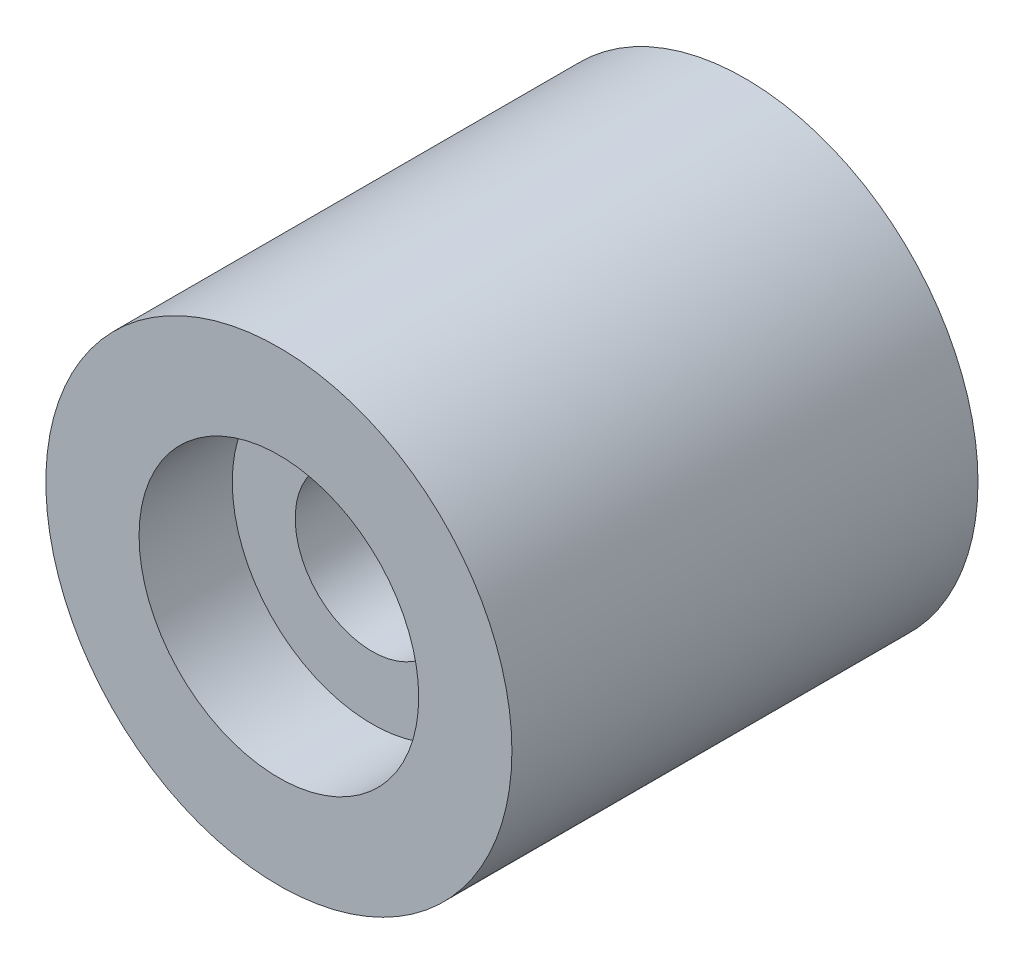
SolidWorks part; units mm, degrees
ref_plane "Front Plane" through (0, 0, 0) normal (0, 0, 1) x (1, 0, 0)
ref_plane "Top Plane" through (0, 0, 0) normal (0, 1, 0) x (1, 0, 0)
ref_plane "Right Plane" through (0, 0, 0) normal (1, 0, 0) x (0, 0, -1)
sketch "Sketch1" plane through (0, 0, 0) normal (0, 0, 1) x (1, 0, 0)
  circle A0 centre (0, 0) radius 5
  dimension "D1" = 10
extrude "Boss-Extrude1" add sketch "Sketch1" along normal blind 10
sketch "Sketch2" plane through (0, 0, 0) normal (0, 0, 1) x (1, 0, 0)
  circle A0 centre (0, 0) radius 3
  dimension "D1" = 6
extrude "Cut-Extrude1" cut sketch "Sketch2" along normal blind 2
sketch "Sketch3" plane through (0, 0, 0) normal (0, 0, 1) x (1, 0, 0)
  circle A0 centre (0, 0) radius 1.65
  dimension "D1" = 3.3
extrude "Cut-Extrude2" cut sketch "Sketch3" along normal blind 14
ref_plane "Plane1" through (0, 0, 10) normal (0, 0, 1) x (1, 0, 0)
sketch "Sketch4" plane through (0, 0, 10) normal (0, 0, 1) x (1, 0, 0)
  circle A0 centre (0, 0) radius 3
  dimension "D1" = 6
extrude "Cut-Extrude3" cut sketch "Sketch4" against normal blind 2
